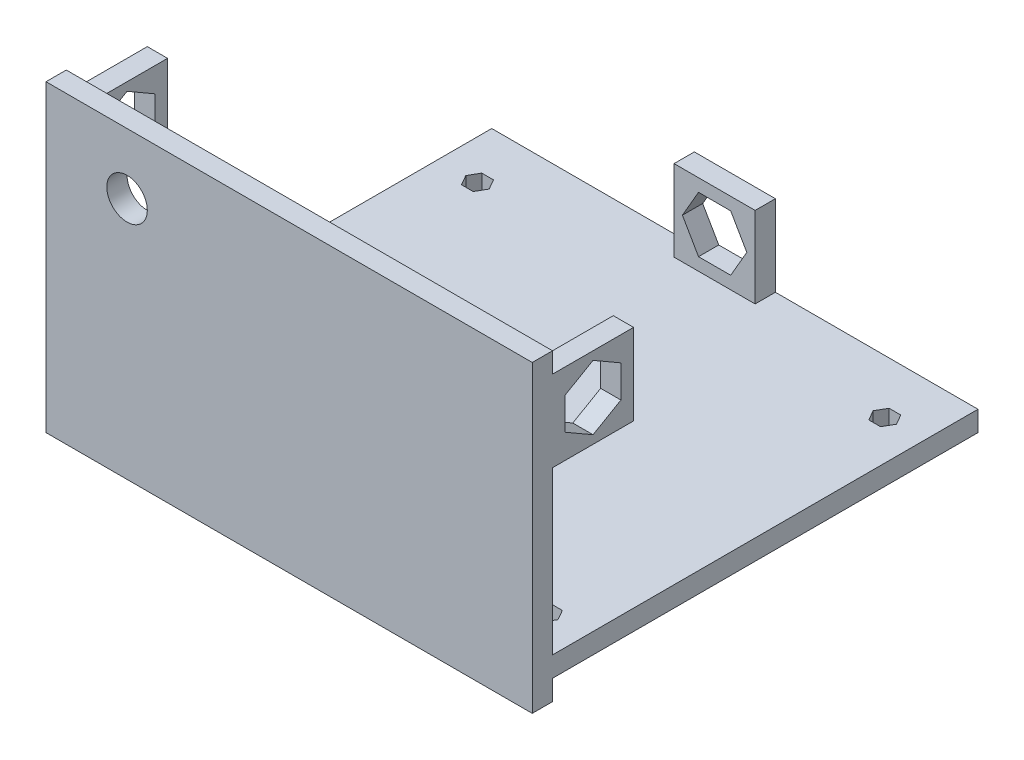
SolidWorks part; units mm, degrees
ref_plane "Front Plane" through (0, 0, 0) normal (0, 0, 1) x (1, 0, 0)
ref_plane "Top Plane" through (0, 0, 0) normal (0, 1, 0) x (1, 0, 0)
ref_plane "Right Plane" through (0, 0, 0) normal (1, 0, 0) x (0, 0, -1)
sketch "Sketch1" plane through (0, 0, 0) normal (0, 0, 1) x (1, 0, 0)
  line L1 (-38.1, -23.8125) -> (38.1, -23.8125)
  line L2 (-38.1, -23.8125) -> (-38.1, 23.8125)
  line L3 (-38.1, 23.8125) -> (38.1, 23.8125)
  line L4 (38.1, -23.8125) -> (38.1, 23.8125)
  line L5 (-38.1, -23.8125) -> (38.1, 23.8125) construction
  line L6 (-38.1, 23.8125) -> (38.1, -23.8125) construction
  point P0 (0, 0)
  dimension "D1" = 76.2
  dimension "D2" = 47.625
extrude "Boss-Extrude1" add sketch "Sketch1" along normal blind 3.175
sketch "Sketch2" plane through (0, 0, 0) normal (0, 0, -1) x (-1, 0, 0)
  line L0 (-38.1, -23.8125) -> (-38.1, 23.8125) construction
  line L1 (-38.1, -20.6375) -> (38.1, -20.6375)
  line L2 (-38.1, -20.6375) -> (-38.1, -17.4625)
  line L3 (-38.1, -17.4625) -> (38.1, -17.4625)
  line L4 (38.1, -20.6375) -> (38.1, -17.4625)
  line L5 (38.1, 23.8125) -> (38.1, -23.8125) construction
  line L6 (38.1, -23.8125) -> (-38.1, -23.8125) construction
  dimension "D1" = 3.175
  dimension "D2" = 3.175
extrude "Boss-Extrude2" add sketch "Sketch2" along normal blind 66.675
sketch "Sketch6" plane through (38.1, 0, 0) normal (1, 0, 0) x (0, 0, -1)
  line L0 (0, -17.4625) -> (0, 23.8125) construction
  line L1 (0, 20.6375) -> (12.7, 20.6375)
  line L2 (0, 20.6375) -> (0, 7.9375)
  line L3 (0, 7.9375) -> (12.7, 7.9375)
  line L4 (12.7, 20.6375) -> (12.7, 7.9375)
  line L5 (-3.175, 23.8125) -> (0, 23.8125) construction
  dimension "D1" = 12.7
  dimension "D2" = 12.7
  dimension "D3" = 3.175
extrude "Boss-Extrude4" add sketch "Sketch6" against normal blind 3.175
sketch "Sketch7" plane through (-38.1, 0, 0) normal (-1, 0, 0) x (0, 0, 1)
  line L0 (0, 23.8125) -> (0, -17.4625) construction
  line L1 (0, 7.9375) -> (-12.7, 7.9375)
  line L2 (0, 7.9375) -> (0, 20.6375)
  line L3 (0, 20.6375) -> (-12.7, 20.6375)
  line L4 (-12.7, 7.9375) -> (-12.7, 20.6375)
  dimension "D1" = 12.7
  dimension "D2" = 12.7
  dimension "D3" = 3.175
extrude "Boss-Extrude5" add sketch "Sketch7" against normal blind 3.175
sketch "Sketch8" plane through (0, 0, -66.675) normal (0, 0, -1) x (-1, 0, 0)
  line L0 (38.1, -17.4625) -> (-38.1, -17.4625) construction
  line L1 (-6.35, -17.4625) -> (6.35, -17.4625)
  line L2 (-6.35, -17.4625) -> (-6.35, -4.7625)
  line L3 (-6.35, -4.7625) -> (6.35, -4.7625)
  line L4 (6.35, -17.4625) -> (6.35, -4.7625)
  point P6 (0, -17.4625)
  dimension "D1" = 12.7
  dimension "D2" = 12.7
extrude "Boss-Extrude6" add sketch "Sketch8" against normal blind 3.175
sketch "Sketch9" plane through (0, 0, -66.675) normal (0, 0, -1) x (-1, 0, 0)
  line L1 (2.5223, -6.7437) -> (-2.5223, -6.7437)
  line L2 (-2.5223, -6.7437) -> (-5.0447, -11.1125)
  line L3 (-5.0447, -11.1125) -> (-2.5223, -15.4813)
  line L4 (-2.5223, -15.4813) -> (2.5223, -15.4813)
  line L5 (2.5223, -15.4813) -> (5.0447, -11.1125)
  line L6 (5.0447, -11.1125) -> (2.5223, -6.7437)
  line L8 (6.35, -4.7625) -> (-6.35, -4.7625) construction
  line L9 (-6.35, -4.7625) -> (-6.35, -17.4625) construction
  circle A0 centre (0, -11.1125) radius 4.3688 construction
  dimension "D1" = 8.7376
  dimension "D2" = 6.35
  dimension "D3" = 6.35
extrude "Cut-Extrude4" cut sketch "Sketch9" against normal blind 3.175 contours L1 L2 L3 L4 L5 L6
sketch "Sketch10" plane through (38.1, 0, 0) normal (1, 0, 0) x (0, 0, -1)
  line L0 (12.7, 20.6375) -> (0, 20.6375) construction
  line L1 (10.7188, 11.7652) -> (10.7188, 16.8098)
  line L2 (10.7188, 16.8098) -> (6.35, 19.3322)
  line L3 (6.35, 19.3322) -> (1.9812, 16.8098)
  line L4 (1.9812, 16.8098) -> (1.9812, 11.7652)
  line L5 (1.9812, 11.7652) -> (6.35, 9.2428)
  line L6 (6.35, 9.2428) -> (10.7188, 11.7652)
  line L7 (12.7, 7.9375) -> (12.7, 20.6375) construction
  circle A0 centre (6.35, 14.2875) radius 4.3688 construction
  dimension "D1" = 8.7376
  dimension "D2" = 6.35
  dimension "D3" = 6.35
extrude "Cut-Extrude5" cut sketch "Sketch10" against normal through all both and the other way through all
sketch "Sketch11" plane through (0, 0, 3.175) normal (0, 0, 1) x (1, 0, 0)
  line L0 (-38.1, 23.8125) -> (-38.1, 20.6375) construction
  line L1 (38.1, 23.8125) -> (-38.1, 23.8125) construction
  circle A0 centre (-25.4, 14.2875) radius 3.175
  dimension "D1" = 6.35
  dimension "D2" = 12.7
  dimension "D3" = 9.525
extrude "Cut-Extrude6" cut sketch "Sketch11" against normal blind 3.175
sketch "Sketch12" plane through (0, -17.4625, 0) normal (0, 1, 0) x (1, 0, 0)
  line L0 (6.35, 66.675) -> (38.1, 66.675) construction
  line L1 (-8.9832, 5.5499) -> (-8.0666, 3.9624)
  line L2 (-8.0666, 3.9624) -> (-6.2336, 3.9624)
  line L3 (-6.2336, 3.9624) -> (-5.317, 5.5499)
  line L4 (-5.317, 5.5499) -> (-6.2336, 7.1374)
  line L5 (-6.2336, 7.1374) -> (-8.0666, 7.1374)
  line L6 (-8.0666, 7.1374) -> (-8.9832, 5.5499)
  line L7 (-38.1, 66.675) -> (-6.35, 66.675) construction
  line L8 (32.8316, 3.6322) -> (33.7482, 5.2197)
  line L9 (33.7482, 5.2197) -> (32.8316, 6.8072)
  line L10 (32.8316, 6.8072) -> (30.9986, 6.8072)
  line L11 (30.9986, 6.8072) -> (30.082, 5.2197)
  line L12 (30.082, 5.2197) -> (30.9986, 3.6322)
  line L13 (30.9986, 3.6322) -> (32.8316, 3.6322)
  line L14 (33.7482, 58.2549) -> (32.8316, 59.8424)
  line L15 (32.8316, 59.8424) -> (30.9986, 59.8424)
  line L16 (30.9986, 59.8424) -> (30.082, 58.2549)
  line L17 (30.082, 58.2549) -> (30.9986, 56.6674)
  line L18 (30.9986, 56.6674) -> (32.8316, 56.6674)
  line L19 (32.8316, 56.6674) -> (33.7482, 58.2549)
  line L20 (-30.9986, 29.3624) -> (-32.8316, 29.3624)
  line L21 (-32.8316, 29.3624) -> (-33.7482, 27.7749)
  line L22 (-33.7482, 27.7749) -> (-32.8316, 26.1874)
  line L23 (-32.8316, 26.1874) -> (-30.9986, 26.1874)
  line L24 (-30.9986, 26.1874) -> (-30.082, 27.7749)
  line L25 (-30.082, 27.7749) -> (-30.9986, 29.3624)
  line L26 (-34.925, 0) -> (-34.925, 12.7) construction
  line L27 (-30.082, 58.2549) -> (-30.9986, 59.8424)
  line L28 (-30.9986, 59.8424) -> (-32.8316, 59.8424)
  line L29 (-32.8316, 59.8424) -> (-33.7482, 58.2549)
  line L30 (-33.7482, 58.2549) -> (-32.8316, 56.6674)
  line L31 (-32.8316, 56.6674) -> (-30.9986, 56.6674)
  line L32 (-30.9986, 56.6674) -> (-30.082, 58.2549)
  line L33 (-38.1, 0) -> (38.1, 0) construction
  circle A0 centre (-7.1501, 5.5499) radius 1.5875 construction
  circle A1 centre (31.9151, 5.2197) radius 1.5875 construction
  circle A2 centre (31.9151, 58.2549) radius 1.5875 construction
  circle A3 centre (-31.9151, 27.7749) radius 1.5875 construction
  circle A4 centre (-31.9151, 58.2549) radius 1.5875 construction
  point P10 (-34.1249, 3.0099)
  dimension "D10" = 3.175
  dimension "D7" = 3.175
  dimension "D4" = 3.175
  dimension "D11" = 3.175
  dimension "D14" = 3.175
  dimension "D2" = 2.54
  dimension "D3" = 26.9748
  dimension "D5" = 2.2098
  dimension "D6" = 66.04
  dimension "D8" = 55.245
  dimension "D9" = 66.04
  dimension "D12" = 2.2098
  dimension "D13" = 24.765
  dimension "D15" = 2.2098
  dimension "D16" = 55.245
  dimension "D17" = 0.8001
  dimension "D18" = 3.0099
extrude "Cut-Extrude7" cut sketch "Sketch12" against normal blind 3.175
